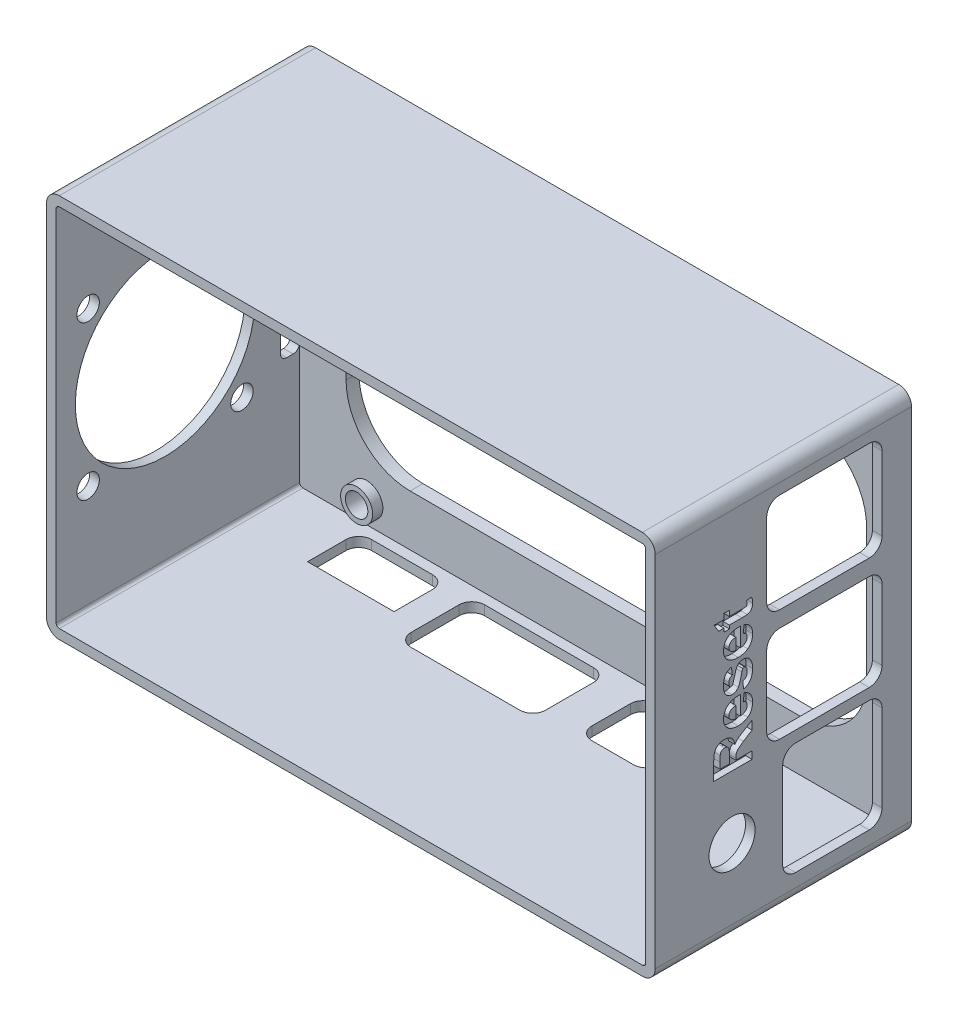
SolidWorks part; units mm, degrees
ref_plane "Top" through (0, 0, 0) normal (0, 0, 1) x (1, 0, 0)
ref_plane "Front" through (0, 0, 0) normal (0, 1, 0) x (1, 0, 0)
ref_plane "Right Plane" through (0, 0, 0) normal (1, 0, 0) x (0, 0, -1)
sketch "Sketch1" plane through (0, 0, 0) normal (0, 0, 1) x (1, 0, 0)
  line L1 (2, 0) -> (93, 0)
  line L2 (0, 2) -> (0, 58)
  line L3 (2, 60) -> (93, 60)
  line L4 (95, 2) -> (95, 58)
  circle A0 centre (12, 54) radius 1.75
  circle A1 centre (12, 5) radius 1.75
  circle A2 centre (70, 5) radius 1.75
  circle A3 centre (70, 54) radius 1.75
  arc A4 (93, 60) -> (95, 58) centre (93, 58) cw
  arc A5 (93, 0) -> (95, 2) centre (93, 2) ccw
  arc A6 (2, 0) -> (0, 2) centre (2, 2) cw
  arc A7 (0, 58) -> (2, 60) centre (2, 58) cw
  point P22 (95, 0)
  point P25 (0, 0)
  point P28 (0, 60)
  dimension "D6" = 3.5
  dimension "D9" = 2
  dimension "D1" = 60
  dimension "D2" = 95
  dimension "D3" = 58
  dimension "D4" = 58
  dimension "D5" = 49
  dimension "D7" = 25
  dimension "D8" = 5
extrude "Boss-Extrude1" add sketch "Sketch1" along normal blind 40
sketch "Sketch3" plane through (0, 0, 40) normal (0, 0, 1) x (1, 0, 0)
  line L8 (93, 58.5) -> (2, 58.5)
  line L9 (1.5, 58) -> (1.5, 2)
  line L10 (2, 1.5) -> (93, 1.5)
  line L11 (93.5, 2) -> (93.5, 58)
  line L12 (93, 58.5) -> (2, 58.5)
  line L13 (1.5, 58) -> (1.5, 2)
  line L14 (2, 1.5) -> (93, 1.5)
  line L15 (93.5, 2) -> (93.5, 58)
  arc A8 (93.5, 58) -> (93, 58.5) centre (93, 58) ccw
  arc A9 (2, 58.5) -> (1.5, 58) centre (2, 58) ccw
  arc A10 (1.5, 2) -> (2, 1.5) centre (2, 2) ccw
  arc A11 (93, 1.5) -> (93.5, 2) centre (93, 2) ccw
  arc A12 (93.5, 58) -> (93, 58.5) centre (93, 58) ccw
  arc A13 (2, 58.5) -> (1.5, 58) centre (2, 58) ccw
  arc A14 (1.5, 2) -> (2, 1.5) centre (2, 2) ccw
  arc A15 (93, 1.5) -> (93.5, 2) centre (93, 2) ccw
  dimension "D1" = 1.5
extrude "Cut-Extrude1" cut sketch "Sketch3" against normal blind 38
sketch "Sketch4" plane through (95, 0, 0) normal (1, 0, 0) x (0, 0, -1)
  line L4 (-19.1, 5.0776) -> (-19.1, 21.0775) construction
  line L5 (-18.1, 4.0776) -> (-6.6, 4.0776)
  line L6 (-20.1, 6.0776) -> (-20.1, 19.5775)
  line L7 (-18.1, 21.5775) -> (-6.6, 21.5775)
  line L8 (-4.6, 6.0776) -> (-4.6, 19.5775)
  line L9 (-20.6, 23.326) -> (-6.6, 23.326)
  line L10 (-22.6, 25.326) -> (-22.6, 36.3259)
  line L11 (-20.6, 38.3259) -> (-6.6, 38.3259)
  line L12 (-4.6, 25.326) -> (-4.6, 36.3259)
  line L13 (-20.6, 40.8259) -> (-6.6, 40.8259)
  line L14 (-22.6, 42.8259) -> (-22.6, 54.3259)
  line L15 (-20.6, 56.3259) -> (-6.6, 56.3259)
  line L16 (-4.6, 42.8259) -> (-4.6, 54.3259)
  line L17 (-19.1, 5.0776) -> (-5.6, 5.0776) construction
  line L18 (-19.1, 21.0775) -> (-5.6, 21.0775) construction
  line L19 (-5.6, 5.0776) -> (-5.6, 21.0775) construction
  line L20 (-21.6, 23.826) -> (-5.6, 23.826) construction
  line L21 (-21.6, 23.826) -> (-21.6, 37.3259) construction
  line L22 (-21.6, 37.3259) -> (-5.6, 37.3259) construction
  line L23 (-5.6, 23.826) -> (-5.6, 37.3259) construction
  line L24 (-21.6, 41.8259) -> (-5.6, 41.8259) construction
  line L25 (-21.6, 41.8259) -> (-21.6, 55.3259) construction
  line L26 (-21.6, 55.3259) -> (-5.6, 55.3259) construction
  line L27 (-5.6, 41.8259) -> (-5.6, 55.3259) construction
  arc A0 (-6.6, 4.0776) -> (-4.6, 6.0776) centre (-6.6, 6.0776) ccw
  arc A1 (-6.6, 21.5775) -> (-4.6, 19.5775) centre (-6.6, 19.5775) cw
  arc A2 (-6.6, 23.326) -> (-4.6, 25.326) centre (-6.6, 25.326) ccw
  arc A3 (-6.6, 38.3259) -> (-4.6, 36.3259) centre (-6.6, 36.3259) cw
  arc A4 (-6.6, 40.8259) -> (-4.6, 42.8259) centre (-6.6, 42.8259) ccw
  arc A5 (-6.6, 56.3259) -> (-4.6, 54.3259) centre (-6.6, 54.3259) cw
  arc A6 (-22.6, 54.3259) -> (-20.6, 56.3259) centre (-20.6, 54.3259) cw
  arc A7 (-20.6, 40.8259) -> (-22.6, 42.8259) centre (-20.6, 42.8259) cw
  arc A8 (-22.6, 36.3259) -> (-20.6, 38.3259) centre (-20.6, 36.3259) cw
  arc A9 (-20.6, 23.326) -> (-22.6, 25.326) centre (-20.6, 25.326) cw
  arc A10 (-20.1, 19.5775) -> (-18.1, 21.5775) centre (-18.1, 19.5775) cw
  arc A11 (-18.1, 4.0776) -> (-20.1, 6.0776) centre (-18.1, 6.0776) cw
  dimension "D13" = 2
  dimension "D1" = 1
  dimension "D2" = 1
  dimension "D3" = 0.5
  dimension "D4" = 1
  dimension "D5" = 0.5
  dimension "D6" = 1
  dimension "D7" = 1
  dimension "D8" = 1
  dimension "D9" = 1
  dimension "D10" = 1
  dimension "D11" = 1
  dimension "D12" = 1
extrude "Cut-Extrude2" cut sketch "Sketch4" against normal blind 2
sketch "Sketch5" plane through (0, 0, 0) normal (0, -1, 0) x (1, 0, 0)
  line L0 (90.3433, 3.6) -> (11.3436, 3.6) construction
  line L1 (12.3413, 11.6) -> (25.8413, 11.6)
  line L2 (12.3413, 11.6) -> (12.3413, 5.6)
  line L3 (14.3413, 3.6) -> (23.8413, 3.6)
  line L4 (25.8413, 11.6) -> (25.8413, 5.6)
  line L5 (15.3413, 8.6) -> (15.3413, 5.6) construction
  line L6 (58.7232, 13.6) -> (65.2232, 13.6)
  line L7 (56.7232, 11.6) -> (56.7232, 5.6)
  line L8 (58.7232, 3.6) -> (65.2232, 3.6)
  line L9 (67.2232, 11.6) -> (67.2232, 5.6)
  line L10 (31.9793, 15.1) -> (48.9792, 15.1)
  line L11 (29.9793, 13.1) -> (29.9793, 5.6)
  line L12 (31.9793, 3.6) -> (48.9792, 3.6)
  line L13 (50.9792, 13.1) -> (50.9792, 5.6)
  line L14 (22.8413, 8.6) -> (22.8413, 5.6) construction
  line L15 (22.8413, 8.6) -> (15.3413, 8.6) construction
  line L19 (32.9793, 12.1) -> (32.9793, 5.6) construction
  line L20 (47.9792, 12.1) -> (47.9792, 5.6) construction
  line L21 (47.9792, 12.1) -> (32.9793, 12.1) construction
  line L22 (47.9792, 5.6) -> (32.9793, 5.6) construction
  line L23 (65.2232, 11.6) -> (58.7232, 11.6) construction
  line L24 (65.2232, 5.6) -> (58.7232, 5.6) construction
  line L25 (58.7232, 11.6) -> (58.7232, 5.6) construction
  line L26 (65.2232, 11.6) -> (65.2232, 5.6) construction
  arc A0 (23.8413, 3.6) -> (25.8413, 5.6) centre (23.8413, 5.6) ccw
  arc A1 (12.3413, 5.6) -> (14.3413, 3.6) centre (14.3413, 5.6) ccw
  arc A2 (65.2232, 13.6) -> (67.2232, 11.6) centre (65.2232, 11.6) cw
  arc A3 (65.2232, 3.6) -> (67.2232, 5.6) centre (65.2232, 5.6) ccw
  arc A4 (56.7232, 5.6) -> (58.7232, 3.6) centre (58.7232, 5.6) ccw
  arc A5 (58.7232, 13.6) -> (56.7232, 11.6) centre (58.7232, 11.6) ccw
  arc A6 (48.9792, 3.6) -> (50.9792, 5.6) centre (48.9792, 5.6) ccw
  arc A7 (29.9793, 5.6) -> (31.9793, 3.6) centre (31.9793, 5.6) ccw
  arc A8 (48.9792, 15.1) -> (50.9792, 13.1) centre (48.9792, 13.1) cw
  arc A9 (31.9793, 15.1) -> (29.9793, 13.1) centre (31.9793, 13.1) ccw
  point P22 (25.8413, 3.6)
  dimension "D12" = 2
  dimension "D1" = 3
  dimension "D2" = 3
  dimension "D3" = 3
  dimension "D4" = 3
  dimension "D5" = 3
  dimension "D6" = 3
  dimension "D7" = 2
  dimension "D8" = 2
  dimension "D9" = 2
  dimension "D10" = 2
  dimension "D11" = 2
extrude "Cut-Extrude3" cut sketch "Sketch5" against normal blind 2
sketch "Sketch6" plane through (0, 0, 0) normal (0, 0, -1) x (-1, 0, 0)
  line L0 (-95, 2) -> (-95, 58) construction
  line L1 (-80, 9.4664) -> (-18.7528, 9.4664)
  line L2 (-90, 19.4664) -> (-90, 40.1534)
  line L3 (-80, 50.1534) -> (-18.7528, 50.1534)
  line L4 (-8.7528, 19.4664) -> (-8.7528, 40.1534)
  arc A0 (-18.7528, 9.4664) -> (-8.7528, 19.4664) centre (-18.7528, 19.4664) ccw
  arc A1 (-18.7528, 50.1534) -> (-8.7528, 40.1534) centre (-18.7528, 40.1534) cw
  arc A2 (-90, 40.1534) -> (-80, 50.1534) centre (-80, 40.1534) cw
  arc A3 (-80, 9.4664) -> (-90, 19.4664) centre (-80, 19.4664) cw
  dimension "D1" = 10
  dimension "D2" = 5
extrude "Cut-Extrude4" cut sketch "Sketch6" against normal blind 2
sketch "Sketch7" plane through (0, 0, 2) normal (0, 0, 1) x (1, 0, 0)
  circle A0 centre (12, 54) radius 2.5
  circle A1 centre (12, 54) radius 1.75
  circle A2 centre (70, 54) radius 2.5
  circle A3 centre (70, 54) radius 1.75
  circle A4 centre (70, 5) radius 2.5
  circle A5 centre (70, 5) radius 1.75
  circle A6 centre (12, 5) radius 2.5
  circle A7 centre (12, 5) radius 1.75
  dimension "D1" = 3.5
  dimension "D2" = 5
extrude "Boss-Extrude2" add sketch "Sketch7" along normal blind 1.6
sketch "Sketch8" plane through (0, 0, 0) normal (-1, 0, 0) x (0, 0, 1)
  line L0 (0, 40.1534) -> (0, 19.4664) construction
  line L1 (4, 40.4599) -> (3, 40.4599)
  line L2 (5, 39.4599) -> (5, 20.86)
  line L3 (4, 19.86) -> (3, 19.86)
  line L4 (2, 39.4599) -> (2, 20.86)
  line L5 (3, 22.86) -> (3.6, 22.86) construction
  line L6 (3, 37.4599) -> (3.6, 37.4599) construction
  arc A0 (3, 19.86) -> (2, 20.86) centre (3, 20.86) cw
  arc A1 (5, 20.86) -> (4, 19.86) centre (4, 20.86) cw
  arc A2 (4, 40.4599) -> (5, 39.4599) centre (4, 39.4599) cw
  arc A3 (3, 40.4599) -> (2, 39.4599) centre (3, 39.4599) ccw
  point P12 (2, 19.86)
  point P15 (5, 19.86)
  dimension "D5" = 1
  dimension "D1" = 2
  dimension "D2" = 3
  dimension "D3" = 3
  dimension "D4" = 3
extrude "Cut-Extrude5" cut sketch "Sketch8" against normal blind 2
sketch "Sketch10" plane through (95, 90, 0) normal (-1, 0, 0) x (0, -1, 0)
  line L0 (88, 40) -> (32, 40) construction
  line L1 (32, 40) -> (32, 0) construction
  circle A0 centre (77, 28) radius 3.6
  dimension "D1" = 7.2
  dimension "D2" = 45
  dimension "D3" = 12
extrude "Cut-Extrude8" cut sketch "Sketch10" along normal up to next
sketch "Sketch11" plane through (0, 0, 0) normal (-1, 0, 0) x (0, 0, 1)
  line L0 (35, 42) -> (11, 18) construction
  line L1 (11, 42) -> (35, 18) construction
  line L2 (40, 60) -> (0, 60) construction
  line L3 (40, 58) -> (40, 2) construction
  circle A0 centre (35, 42) radius 1.75
  circle A1 centre (11, 42) radius 1.75
  circle A2 centre (11, 18) radius 1.75
  circle A3 centre (35, 18) radius 1.75
  circle A4 centre (23, 30) radius 14
  dimension "D4" = 3.5
  dimension "D5" = 28
  dimension "D1" = 24
  dimension "D2" = 24
  dimension "D3" = 24
  dimension "D6" = 30
  dimension "D7" = 17
extrude "Cut-Extrude10" cut sketch "Sketch11" against normal up to next
sketch "Sketch14" plane through (95, 0, 0) normal (1, 0, 0) x (0, 0, -1)
  line L0 (-24.8772, 22.1441) -> (-24.8772, 50.818) construction
  text T0 "Reset" font "Arial" height 6
  point P3 (-25.6628, 21.9477)
  point P4 (-24.8772, 22.1441)
extrude "Cut-Extrude11" cut sketch "Sketch14" against normal blind 1
sketch "Sketch15" plane through (0, 0, 0) normal (0, -1, 0) x (1, 0, 0)
  line L0 (9.5003, 12.854) -> (27.9947, 12.854) construction
  text T0 "+5V DC"
  point P3 (5.7871, 16.7814)
  point P4 (9.0004, 12.9968)
  point P5 (0, 0)
  point P6 (27.9947, 12.9968)
  point P7 (10.6428, 13.1396)
  point P8 (10.2143, 13.4253)
  point P9 (9.5003, 12.854)
extrude "Cut-Extrude12" cut sketch "Sketch15" against normal blind 1
